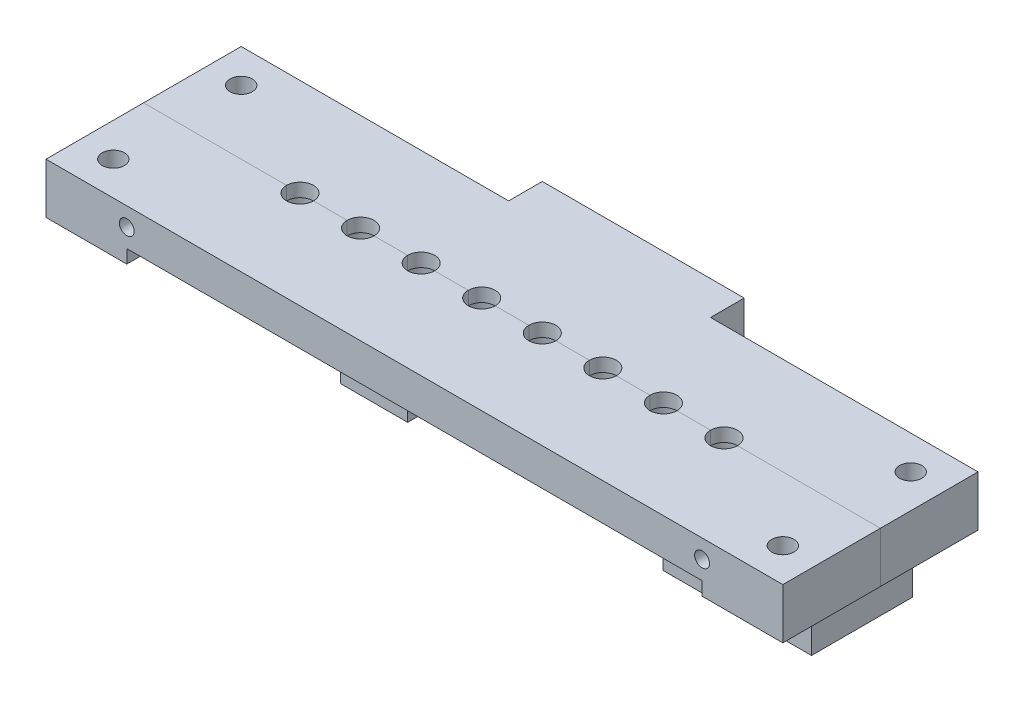
SolidWorks part; units mm, degrees
ref_plane "Front Plane" through (0, 0, 0) normal (0, 0, 1) x (1, 0, 0)
ref_plane "Top Plane" through (0, 0, 0) normal (0, 1, 0) x (1, 0, 0)
ref_plane "Right Plane" through (0, 0, 0) normal (1, 0, 0) x (0, 0, -1)
sketch "Sketch1" plane through (0, 0, 0) normal (0, 0, 1) x (1, 0, 0)
  line L0 (-31.5, 3.75) -> (-31.5, -3.75) construction
  line L1 (54.74, -3.75) -> (-54.74, -3.75)
  line L2 (54.74, -3.75) -> (54.74, 3.75)
  line L3 (54.74, 3.75) -> (-54.74, 3.75)
  line L4 (-54.74, -3.75) -> (-54.74, 3.75)
  line L5 (54.74, -3.75) -> (-54.74, 3.75) construction
  line L6 (54.74, 3.75) -> (-54.74, -3.75) construction
  line L7 (-33.5, 3.75) -> (-33.5, 1.75)
  line L8 (-33.5, -1.25) -> (-34.25, -1.25)
  line L9 (-34.25, -1.25) -> (-34.25, 1.75)
  line L10 (-34.25, 1.75) -> (-33.5, 1.75)
  line L11 (-33.5, -1.25) -> (-33.5, -2.25)
  line L12 (-33.5, -2.25) -> (-35.4, -2.25)
  line L13 (-35.4, -2.25) -> (-35.4, -3.75)
  point P0 (0, 0)
  point P17 (-34.25, 0.25)
  dimension "D1" = 109.48
  dimension "D2" = 23.24
  dimension "D3" = 5.5
  dimension "D4" = 4
  dimension "D5" = 7.8
  dimension "D6" = 4
  dimension "D7" = 3
  dimension "D8" = 2
  dimension "D9" = 1
extrude "Boss-Extrude1" add sketch "Sketch1" along normal mid plane 29 contours L13 L12 L11 L8 L9 L10 L7 L3 L4 L1 | L12 L13 L1 L2 L3 L7 L10 L9 L8 L11
sketch "Sketch2" plane through (0, 0, 0) normal (0, 0, 1) x (1, 0, 0)
  line L0 (-31.5, 3.75) -> (-31.5, -3.75) construction
  line L1 (-35.4, -2.25) -> (-35.4, -3.75) construction
  line L2 (-33.5, -2.25) -> (-35.4, -2.25) construction
  line L3 (-33.5, -1.25) -> (-33.5, -2.25) construction
  line L4 (-33.5, -1.25) -> (-34.25, -1.25) construction
  line L5 (-34.25, -1.25) -> (-34.25, 1.75) construction
  line L6 (-34.25, 1.75) -> (-33.5, 1.75) construction
  line L7 (-33.5, 3.75) -> (-33.5, 1.75) construction
  line L8 (-31.5, 3.75) -> (-31.5, -3.75)
  line L9 (-35.4, -2.25) -> (-35.4, -3.75)
  line L10 (-33.5, -2.25) -> (-35.4, -2.25)
  line L11 (-33.5, -1.25) -> (-33.5, -2.25)
  line L12 (-33.5, -1.25) -> (-34.25, -1.25)
  line L13 (-34.25, -1.25) -> (-34.25, 1.75)
  line L14 (-34.25, 1.75) -> (-33.5, 1.75)
  line L15 (-33.5, 3.75) -> (-33.5, 1.75)
  line L16 (-33.5, 3.75) -> (-31.5, 3.75)
  line L17 (-31.5, -3.75) -> (-35.4, -3.75)
revolve "Cut-Revolve2" cut sketch "Sketch2" angle 360 about L8
pattern_linear "LPattern1" count 8 spacing 9 along (1, 0, 0) of "Cut-Revolve2"
sketch "Sketch4" plane through (0, 3.75, 0) normal (0, 1, 0) x (1, 0, 0)
  line L0 (54.74, 14.5) -> (-54.74, 14.5) construction
  line L1 (-54.74, -14.5) -> (-54.74, 14.5) construction
  line L2 (54.74, -14.5) -> (-54.74, -14.5) construction
  line L3 (54.74, -14.5) -> (54.74, 14.5) construction
  circle A0 centre (-49.74, 9.5) radius 1.65
  circle A1 centre (49.74, 9.5) radius 1.65
  circle A2 centre (49.74, -9.5) radius 1.65
  circle A3 centre (-49.74, -9.5) radius 1.65
  dimension "D4" = 3.3
  dimension "D1" = 5
  dimension "D2" = 5
  dimension "D3" = 5
  dimension "D5" = 5
  dimension "D6" = 5
extrude "Cut-Extrude1" cut sketch "Sketch4" against normal up to surface (7.5 mm away) up to face at (31.5, -3.75, 3.9)
sketch "Sketch5" plane through (0, -3.75, 0) normal (0, -1, 0) x (1, 0, 0)
  line L0 (54.74, 14.5) -> (-54.74, 14.5) construction
  line L1 (-42.74, 14.5) -> (42.74, 14.5)
  line L2 (-42.74, 14.5) -> (-42.74, 9.5)
  line L3 (-42.74, 9.5) -> (42.74, 9.5)
  line L4 (42.74, 14.5) -> (42.74, 9.5)
  line L5 (54.74, -14.5) -> (-54.74, -14.5) construction
  line L6 (-42.74, -14.5) -> (42.74, -14.5)
  line L7 (-42.74, -14.5) -> (-42.74, -9.5)
  line L8 (-42.74, -9.5) -> (42.74, -9.5)
  line L9 (42.74, -14.5) -> (42.74, -9.5)
  line L10 (-54.74, 14.5) -> (-54.74, -14.5) construction
  line L11 (54.74, 14.5) -> (54.74, -14.5) construction
  dimension "D1" = 5
  dimension "D2" = 12
  dimension "D3" = 12
extrude "Cut-Extrude2" cut sketch "Sketch5" against normal blind 2
sketch "Sketch7" plane through (0, 0, -14.5) normal (0, 0, -1) x (-1, 0, 0)
  line L0 (-54.74, 3.75) -> (54.74, 3.75) construction
  line L1 (-54.74, -3.75) -> (-66.74, -3.75)
  line L2 (-54.74, -3.75) -> (-54.74, 3.75)
  line L3 (-54.74, 3.75) -> (-66.74, 3.75)
  line L4 (-66.74, -3.75) -> (-66.74, 3.75)
  line L5 (54.74, -3.75) -> (66.74, -3.75)
  line L6 (54.74, -3.75) -> (54.74, 3.75)
  line L7 (54.74, 3.75) -> (66.74, 3.75)
  line L8 (66.74, -3.75) -> (66.74, 3.75)
  circle A0 centre (-60.74, 0) radius 2.15
  circle A1 centre (60.74, 0) radius 2.15
  point P15 (60.74, -3.75)
  point P17 (66.74, 0)
  point P24 (-60.74, 3.75)
  point P26 (-54.74, 0)
  dimension "D3" = 4.3
  dimension "D2" = 12
extrude "Boss-Extrude2" [suppressed] add sketch "Sketch7" against normal up to surface (29 mm away)
sketch "Sketch16" plane through (0, 0, 14.5) normal (0, 0, 1) x (1, 0, 0)
  line L0 (-54.74, -3.75) -> (-54.74, 3.75) construction
  line L3 (54.74, -3.75) -> (54.74, 3.75) construction
  line L4 (-37.8172, 3.75) -> (-37.8172, -1.75) construction
  line L5 (54.74, 3.75) -> (-54.74, 3.75) construction
  line L6 (42.74, -1.75) -> (-42.74, -1.75) construction
  circle A0 centre (-42.74, 1) radius 1.1
  circle A1 centre (42.74, 1) radius 1.1
  point P14 (-37.8172, 1)
  point P15 (0, 0)
  point P16 (0, 0)
  point P17 (0, 0)
  point P18 (0, 0)
  point P19 (0, 0)
  dimension "D1" = 2.2
  dimension "D2" = 12
  dimension "D3" = 12
extrude "Cut-Extrude5" cut sketch "Sketch16" against normal up to surface (29 mm away) up to face at (0, -1.375, -14.5)
sketch "Sketch8" plane through (0, 0, -14.5) normal (0, 0, -1) x (-1, 0, 0)
  line L0 (-54.74, 3.75) -> (54.74, 3.75) construction
  line L1 (-15, 3.75) -> (15, 3.75)
  line L2 (-15, 3.75) -> (-15, -1.75)
  line L3 (-15, -1.75) -> (15, -1.75)
  line L4 (15, 3.75) -> (15, -1.75)
  line L5 (42.74, -1.75) -> (-42.74, -1.75) construction
  point P8 (0, 3.75)
  point P9 (0, 3.75)
  dimension "D1" = 30
extrude "Boss-Extrude3" add sketch "Sketch8" along normal up to surface (5 mm away)
sketch "Sketch9" plane through (0, -1.75, 0) normal (0, -1, 0) x (1, 0, 0)
  line L0 (15, -19.5) -> (15, -14.5) construction
  line L1 (-15, -19.5) -> (15, -19.5) construction
  line L2 (-15, -19.5) -> (-15, -14.5) construction
  line L3 (15, -19.5) -> (15, -14.5)
  line L4 (-15, -19.5) -> (15, -19.5)
  line L5 (-15, -19.5) -> (-15, -14.5)
  line L6 (-15, -14.5) -> (15, -14.5)
extrude "Boss-Extrude4" add sketch "Sketch9" along normal up to surface (25.5 mm away)
sketch "Sketch10" plane through (15, 0, 0) normal (1, 0, 0) x (0, 0, -1)
  line L0 (19.5, -27.25) -> (19.5, 3.75) construction
  line L1 (14.5, -27.25) -> (19.5, -27.25)
  line L2 (14.5, -27.25) -> (14.5, -22.25)
  line L3 (14.5, -22.25) -> (19.5, -22.25)
  line L4 (19.5, -27.25) -> (19.5, -22.25)
  dimension "D1" = 5
extrude "Boss-Extrude5" add sketch "Sketch10" along normal blind 20 and the other way blind 50
sketch "Sketch11" plane through (0, -22.25, 0) normal (0, 1, 0) x (1, 0, 0)
  line L1 (35, 19.5) -> (35, 14.5) construction
  line L2 (-35, 19.5) -> (-35, 14.5) construction
  circle A0 centre (-30, 17) radius 1.65
  circle A1 centre (30, 17) radius 1.65
  point P8 (35, 17)
  dimension "D1" = 3.3
  dimension "D2" = 5
  dimension "D3" = 5
extrude "Cut-Extrude3" cut sketch "Sketch11" against normal up to surface (5 mm away) up to face at (0, -27.25, -17)
sketch "Sketch12" plane through (0, 0, -19.5) normal (0, 0, -1) x (-1, 0, 0)
  line L0 (35, -27.25) -> (-35, -27.25) construction
  line L1 (-35, -22.25) -> (-25, -22.25)
  line L2 (-35, -22.25) -> (-35, -27.25)
  line L3 (-35, -27.25) -> (-25, -27.25)
  line L4 (-25, -22.25) -> (-25, -27.25)
  line L5 (35, -22.25) -> (15, -22.25) construction
  line L6 (35, -27.25) -> (25, -27.25)
  line L7 (35, -27.25) -> (35, -22.25)
  line L8 (35, -22.25) -> (25, -22.25)
  line L9 (25, -27.25) -> (25, -22.25)
  dimension "D1" = 10
  dimension "D2" = 10
extrude "Boss-Extrude6" add sketch "Sketch12" along normal blind 5
sketch "Sketch13" plane through (0, 0, -14.5) normal (0, 0, 1) x (1, 0, 0)
  line L0 (35, -27.25) -> (-35, -27.25) construction
  line L1 (-35, -22.25) -> (-25, -22.25)
  line L2 (-35, -22.25) -> (-35, -27.25)
  line L3 (-35, -27.25) -> (-25, -27.25)
  line L4 (-25, -22.25) -> (-25, -27.25)
  line L5 (15, -22.25) -> (35, -22.25) construction
  line L6 (35, -27.25) -> (25, -27.25)
  line L7 (35, -27.25) -> (35, -22.25)
  line L8 (35, -22.25) -> (25, -22.25)
  line L9 (25, -27.25) -> (25, -22.25)
  line L10 (-25, -22.25) -> (-25, -27.25) construction
  line L11 (25, -27.25) -> (25, -22.25) construction
extrude "Boss-Extrude7" add sketch "Sketch13" along normal blind 5
chamfer "Chamfer2" distance 10 angle 45 2 edges at (-15, -22.25, -17) (15, -22.25, -17)
split "Split1" trim tools "Front Plane" bodies to split 114 resulting bodies 111 112
ref_plane "Plane1" through (0, 0, 0) normal (-1, 0, 0) x (0, 0, 1)
sketch "Sketch14" plane through (0, 0, 0) normal (-1, 0, 0) x (0, 0, 1)
  line L0 (-19.5, -12.25) -> (-27.42, -20.17)
  line L1 (-27.42, -20.17) -> (-27.42, -45.25)
  line L2 (-19.5, 3.75) -> (-19.5, -12.25) construction
  line L3 (-27.42, -33.9626) -> (-27.42, -29.25) construction
  line L4 (-19.5, -12.25) -> (-19.5, -5.1789)
  line L5 (-19.5, -5.1789) -> (-32.42, -18.0989)
  line L6 (-32.42, -18.0989) -> (-32.42, -45.25)
  line L7 (-32.42, -45.25) -> (-27.42, -45.25)
  point P8 (-27.42, -45.25)
  dimension "D1" = 135
  dimension "D2" = 5
  dimension "D3" = 5
extrude "Boss-Extrude8" add sketch "Sketch14" along normal mid plane 10 contours L5 L6 L7 L1 L0 L4
sketch "Sketch15" plane through (0, 0, -32.42) normal (0, 0, -1) x (-1, 0, 0)
  line L0 (5, -45.25) -> (-5, -45.25) construction
  line L1 (100, -38.3428) -> (-170, -38.3428) construction
  line L2 (100, -36.1572) -> (-170, -36.1572) construction
  line L3 (100, -38.3428) -> (-170, -38.3428) construction
  line L4 (100, -36.1572) -> (-170, -36.1572) construction
  line L5 (0, -36.1572) -> (0, -38.3428) construction
  circle A0 centre (0, -37.25) radius 1.65
  point P6 (0, -45.25)
  point P12 (0, -37.25)
  dimension "D1" = 3.3
extrude "Cut-Extrude4" cut sketch "Sketch15" against normal up to surface (5 mm away) up to face at (0, -32.71, -27.42)
equation "\"Plate_height\"= 14.35mm'end to end plate height"
equation "\"Plate_width\"= 85.48mm'end to end plate width"
equation "\"Plate_length\"= 127.76mm'end to end plate length"
equation "\"hole_offset_length_side\"= 11.24mm'offset between well and length side "
equation "\"well2well_distance\"= 9mm'center to center/edge to edge separation between 2 wells"
equation "\"well_diameter\"= 7mm'well diameter"
equation "\"lensL_diameter\"= 3mm'lens diameter on LED side"
equation "\"lensL_height\"= 2mm'lens height on LED side"
equation "\"lensL_focal\"= 4mm'lens focal length on LED side"
equation "\"lensP_diameter\"= 5mm'lens diameter on photodiode side"
equation "\"lensP_height\"= 2mm'lens height on photodiode side"
equation "\"lensP_focal\"= 4mm'lens focal length on photodiode side"
equation "\"filter_length\"= 40mm'filter length"
equation "\"filter_width\"= 25mm'filter width"
equation "\"filter_thickness\"= 2mm'filter thickness"
equation "\"filter2filter_clearance\"= 1.5mm'wall thickness between both filters"
equation "\"LED_diameter\"= 3.45mm'bounding diameter of LED"
equation "\"photodiode_diameter\"= 2.9 * 2mm + 1'bounding diameter of photodiode with optical center aligned with diameter center. Dont forget to align the pcb photodiode with the optical center of your system"
equation "\"D1@Sketch1\"=\"Plate_width\"+2*2+10*2"
equation "\"D2@Sketch1\"=10+2+\"hole_offset_length_side\""
equation "\"D3@Sketch1\"=\"lensP_diameter\"+0.5"
equation "\"D5@Sketch1\"=\"photodiode_diameter\"+0.5*2"
equation "\"D6@Sketch1\"=\"lensL_focal\""
equation "\"D7@Sketch1\"=\"lensL_height\"+0.5*2"
equation "\"D1@Boss-Extrude1\"=\"well2well_distance\"+10*2"
equation "\"D3@LPattern1\"=\"well2well_distance\""
